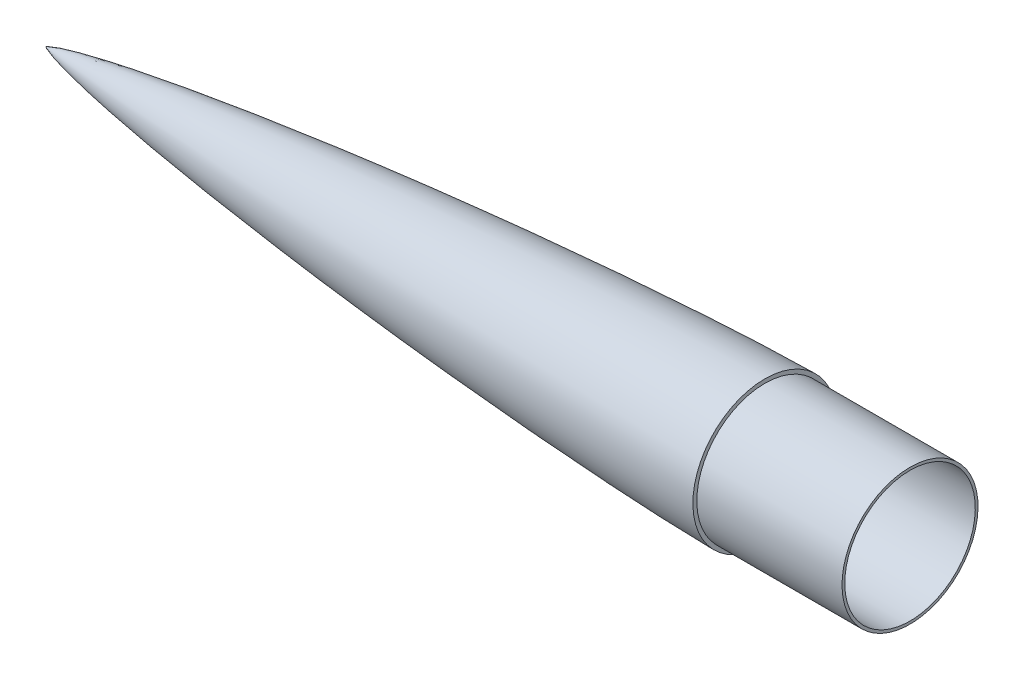
SolidWorks part; units mm, degrees
other "Markup1"
sketch "Sketch5" plane through (0, 27.3, 27.3) normal (0.8928, 0.2893, 0.3454) x (0.366, -0.0189, -0.9304)
other "Markup2"
sketch "Sketch13" plane through (0, -27.3, 27.3) normal (0.8843, -0.0281, 0.466) x (0.4595, -0.1248, -0.8794)
ref_plane "Front Plane" through (0, 0, 0) normal (0, 0, 1) x (1, 0, 0)
ref_plane "Top Plane" through (0, 0, 0) normal (0, 1, 0) x (1, 0, 0)
ref_plane "Right Plane" through (0, 0, 0) normal (1, 0, 0) x (0, 0, -1)
sketch "Sketch1" plane through (0, 0, 0) normal (0, 0, 1) x (1, 0, 0)
  line L0 (0, 35.965) -> (0, 37.465)
  line L1 (0, 37.465) -> (-80, 37.465)
  line L2 (-80, 37.465) -> (-80, 39.624)
  line L3 (-472.2236, 0) -> (-476, 0)
  line L4 (0, 35.965) -> (-144.4765, 35.965)
  line L7 (-144.4765, 35.965) -> (-144.5511, 37.4631) construction
  line L8 (-472.2236, 0) -> (-472.6839, 1.4276) construction
  arc A3 (-472.2236, 0) -> (-144.4765, 35.965) centre (-80, -2062.9596) cw
  spline S0 degree 4 poles (-476, 0) (-475.9999, 0.0009) (-475.9919, 0.0192) (-475.9655, 0.0489) (-475.8808, 0.1235) (-475.7345, 0.2191) (-475.488, 0.357) (-474.9464, 0.6158) (-473.6516, 1.1298) (-471.2902, 1.8875) (-467.9134, 2.8086) (-463.5765, 3.8513) (-458.7988, 4.8961) (-452.5896, 6.156) (-444.699, 7.631) (-435.2676, 9.2575) (-421.4885, 11.4584) (-404.6275, 13.9262) (-384.9233, 16.5692) (-362.3724, 19.3405) (-339.7973, 21.9059) (-317.2026, 24.2918) (-294.5914, 26.5153) (-271.9657, 28.5873) (-249.3273, 30.5139) (-226.6771, 32.2976) (-206.8487, 33.7324) (-189.8465, 34.8692) (-175.6738, 35.7516) (-164.3332, 36.4169) (-152.9902, 37.0395) (-143.063, 37.5444) (-134.5524, 37.9463) (-127.4593, 38.2592) (-121.7842, 38.4954) (-116.8179, 38.689) (-112.5607, 38.8447) (-108.3032, 38.9919) (-104.0953, 39.1283) (-99.2273, 39.2724) (-94.3837, 39.3967) (-90.2745, 39.4872) (-86.8499, 39.5493) (-84.1101, 39.5917) (-82.0551, 39.612) (-80.685, 39.624) (-80, 39.624) knots 0 0 0 0 0 0.000008 0.0002 0.000392 0.001132 0.001756 0.003034 0.00641 0.0151 0.026623 0.038146 0.051157 0.064167 0.090188 0.118682 0.147176 0.204165 0.261153 0.318142 0.37513 0.432119 0.489108 0.546096 0.603085 0.660073 0.717062 0.745556 0.77405 0.802545 0.831039 0.859533 0.87378 0.888027 0.902274 0.916521 0.923645 0.930769 0.945016 0.958762 0.972508 0.979381 0.986254 0.993127 1 1 1 1 1 construction
  spline S1 degree 4 poles (-476, 0) (-475.9999, 0.0009) (-475.9919, 0.0192) (-475.9655, 0.0489) (-475.8808, 0.1235) (-475.7345, 0.2191) (-475.488, 0.357) (-474.9464, 0.6158) (-473.6516, 1.1298) (-471.2902, 1.8875) (-467.9134, 2.8086) (-463.5765, 3.8513) (-458.7988, 4.8961) (-452.5896, 6.156) (-444.699, 7.631) (-435.2676, 9.2575) (-421.4885, 11.4584) (-404.6275, 13.9262) (-384.9233, 16.5692) (-362.3724, 19.3405) (-339.7973, 21.9059) (-317.2026, 24.2918) (-294.5914, 26.5153) (-271.9657, 28.5873) (-249.3273, 30.5139) (-226.6771, 32.2976) (-206.8487, 33.7324) (-189.8465, 34.8692) (-175.6738, 35.7516) (-164.3332, 36.4169) (-152.9902, 37.0395) (-143.063, 37.5444) (-134.5524, 37.9463) (-127.4593, 38.2592) (-121.7842, 38.4954) (-116.8179, 38.689) (-112.5607, 38.8447) (-108.3032, 38.9919) (-104.0953, 39.1283) (-99.2273, 39.2724) (-94.3837, 39.3967) (-90.2745, 39.4872) (-86.8499, 39.5493) (-84.1101, 39.5917) (-82.0551, 39.612) (-80.685, 39.624) (-80, 39.624) knots 0 0 0 0 0 0.000008 0.0002 0.000392 0.001132 0.001756 0.003034 0.00641 0.0151 0.026623 0.038146 0.051157 0.064167 0.090188 0.118682 0.147176 0.204165 0.261153 0.318142 0.37513 0.432119 0.489108 0.546096 0.603085 0.660073 0.717062 0.745556 0.77405 0.802545 0.831039 0.859533 0.87378 0.888027 0.902274 0.916521 0.923645 0.930769 0.945016 0.958762 0.972508 0.979381 0.986254 0.993127 1 1 1 1 1
  dimension "D3" = 80
  dimension "D5" = 1.5
  dimension "D4" = 37.465
  dimension "D1" = 39.624
  dimension "D2" = 1.5
  dimension "D6" = 1.5
  dimension "D7" = 396
revolve "Revolve1" add sketch "Sketch1" angle 360 about L3
ref_plane "Plane1" through (-80, 0, 0) normal (1, 0, 0) x (0, 0, -1)
ref_plane "Plane2" through (-388, 0, 0) normal (1, 0, 0) x (0, 0, -1)
equation "\"ConeLength\" = 396"
equation "\"D3@Sketch1\"= \"ShoulderLength\""
equation "\"ConeDiameter\" = 3.12in"
equation "\"ShoulderLength\" = 8cm"
equation "\"ShoulderDiameter\" = 2.95in"
equation "\"D4@Sketch1\"=\"ShoulderDiameter\"/2"
equation "\"WallThickness\"= .15cm"
equation "\"D5@Sketch1\"=\"WallThickness\""
equation "\"D1@Sketch1\"=\"ConeDiameter\"/2"
equation "\"ShapeParameter\"= 0"
equation "\"D2@Sketch1\"=\"WallThickness\""
equation "\"D6@Sketch1\"=\"WallThickness\""
equation "\"D7@Sketch1\"=\"ConeLength\""
